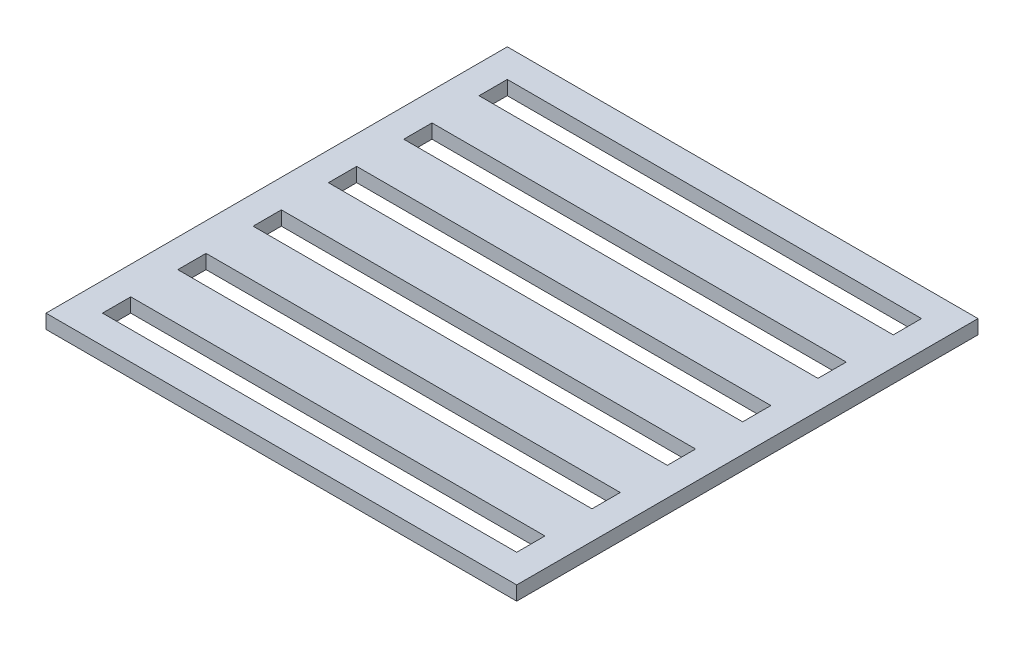
SolidWorks part; units mm, degrees
material "Balsa"
ref_plane "Alzado" through (0, 0, 0) normal (0, 0, 1) x (1, 0, 0)
ref_plane "Planta" through (0, 0, 0) normal (0, 1, 0) x (1, 0, 0)
ref_plane "Vista lateral" through (0, 0, 0) normal (1, 0, 0) x (0, 0, -1)
sketch "Croquis3" plane through (0, 0, 0) normal (1, 0, 0) x (0, 0, -1)
  line L1 (245, -7.5) -> (-245, -7.5)
  line L2 (245, -7.5) -> (245, 7.5)
  line L3 (245, 7.5) -> (-245, 7.5)
  line L4 (-245, -7.5) -> (-245, 7.5)
  line L5 (245, -7.5) -> (-245, 7.5) construction
  line L6 (245, 7.5) -> (-245, -7.5) construction
  point P0 (0, 0)
  dimension "D1" = 15
  dimension "D2" = 490
extrude "Saliente-Extruir1" add sketch "Croquis3" along normal blind 500
sketch "Croquis4" plane through (0, 7.5, 0) normal (0, 1, 0) x (1, 0, 0)
  line L0 (500, 245) -> (0, 245) construction
  line L1 (30, 185) -> (470, 185)
  line L2 (30, 185) -> (30, 215)
  line L3 (30, 215) -> (470, 215)
  line L4 (470, 185) -> (470, 215)
  line L5 (30, 185) -> (470, 215) construction
  line L6 (30, 215) -> (470, 185) construction
  line L7 (0, 245) -> (0, -245) construction
  line L10 (470, 105) -> (30, 105)
  line L11 (470, 105) -> (470, 135)
  line L12 (470, 135) -> (30, 135)
  line L13 (30, 105) -> (30, 135)
  line L14 (470, 105) -> (30, 135) construction
  line L15 (470, 135) -> (30, 105) construction
  line L16 (470, 25) -> (30, 25)
  line L17 (470, 25) -> (470, 55)
  line L18 (470, 55) -> (30, 55)
  line L19 (30, 25) -> (30, 55)
  line L20 (470, 25) -> (30, 55) construction
  line L21 (470, 55) -> (30, 25) construction
  line L22 (470, -55) -> (30, -55)
  line L23 (470, -55) -> (470, -25)
  line L24 (470, -25) -> (30, -25)
  line L25 (30, -55) -> (30, -25)
  line L26 (470, -55) -> (30, -25) construction
  line L27 (470, -25) -> (30, -55) construction
  line L28 (470, -135) -> (30, -135)
  line L29 (470, -135) -> (470, -105)
  line L30 (470, -105) -> (30, -105)
  line L31 (30, -135) -> (30, -105)
  line L32 (470, -135) -> (30, -105) construction
  line L33 (470, -105) -> (30, -135) construction
  line L34 (470, -215) -> (30, -215)
  line L35 (470, -215) -> (470, -185)
  line L36 (470, -185) -> (30, -185)
  line L37 (30, -215) -> (30, -185)
  line L38 (470, -215) -> (30, -185) construction
  line L39 (470, -185) -> (30, -215) construction
  point P0 (250, 200)
  point P11 (250, 120)
  point P16 (250, 40)
  point P21 (250, -40)
  point P26 (250, -120)
  point P31 (250, -200)
  point P36 (0, 0)
  dimension "D1" = 30
  dimension "D2" = 440
  dimension "D3" = 30
  dimension "D4" = 30
  dimension "D5" = 30
  dimension "D6" = 440
  dimension "D7" = 50
  dimension "D8" = 50
  dimension "D9" = 30
  dimension "D10" = 440
  dimension "D11" = 30
  dimension "D12" = 30
  dimension "D13" = 30
  dimension "D14" = 440
  dimension "D15" = 30
  dimension "D16" = 50
  dimension "D17" = 30
  dimension "D18" = 50
  dimension "D19" = 50
  dimension "D20" = 30
  dimension "D21" = 440
  dimension "D22" = 30
  dimension "D23" = 30
  dimension "D24" = 440
extrude "Cortar-Extruir1" cut sketch "Croquis4" against normal blind 15
